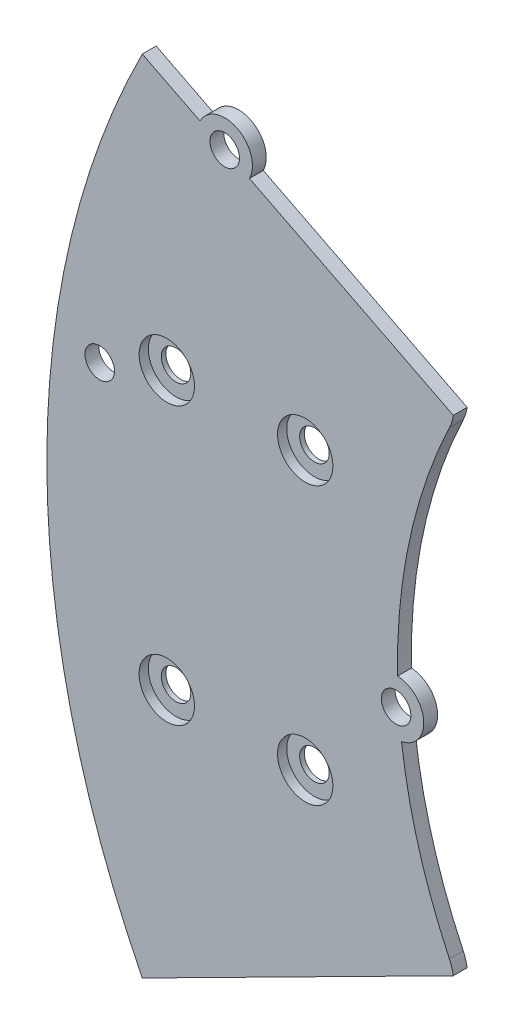
SolidWorks part; units mm, degrees
ref_plane "Front" through (0, 0, 0) normal (0, 0, 1) x (1, 0, 0)
ref_plane "Top" through (0, 0, 0) normal (0, 1, 0) x (1, 0, 0)
ref_plane "Right" through (0, 0, 0) normal (1, 0, 0) x (0, 0, -1)
sketch "Sketch1" plane through (0, 0, 0) normal (0, 0, 1) x (1, 0, 0)
  line L6 (32.7705, 29) -> (-0.1384, 48)
  line L7 (32.7705, -29) -> (-0.1384, -48)
  circle A0 centre (0, 15) radius 1.6
  circle A1 centre (15, 15) radius 1.6
  circle A2 centre (15, -15) radius 1.6
  circle A3 centre (0, -15) radius 1.6
  arc A4 (-0.1384, 48) -> (-0.1384, -48) centre (83, 0) ccw
  arc A5 (32.7705, 29) -> (32.7705, -29) centre (83, 0) ccw
extrude "Boss-Extrude1" add sketch "Sketch1" along normal blind 1.5
fillet "Fillet1" radius 5 4 edges at (32.7705, 29, 0.75) (-0.1384, 48, 0.75) (32.7705, -29, 0.75) (-0.1384, -48, 0.75)
sketch "Sketch2" plane through (0, 0, 1.5) normal (0, 0, 1) x (1, 0, 0)
  line L0 (83, 0) -> (-2.6502, 43.3594)
  line L1 (83, 0) -> (-2.6502, -43.3594)
  line L2 (-2.6502, -43.3594) -> (-16.4497, -74.0903)
  line L3 (-16.4497, -74.0903) -> (122.6028, -61.5432)
  line L4 (122.6028, -61.5432) -> (145.6273, 17.8784)
  line L5 (145.6273, 17.8784) -> (87.9367, 66.5144)
  line L6 (87.9367, 66.5144) -> (-7.0071, 61.211)
  line L7 (-7.0071, 61.211) -> (-2.6502, 43.3594)
extrude "Cut-Extrude1" cut sketch "Sketch2" against normal blind 1.5
sketch "Sketch3" plane through (0, 0, 1.5) normal (0, 0, 1) x (1, 0, 0)
  line L0 (-2.6502, 43.3594) -> (6.2792, 38.839)
  line L1 (-2.6502, 43.3594) -> (31.0524, 26.2979) construction
  line L2 (6.2792, 38.839) -> (-7.2706, 12.0733)
  line L3 (-7.2706, 12.0733) -> (24.8482, -4.1864)
  circle A0 centre (6.2792, 38.839) radius 1.6
  circle A1 centre (-7.2706, 12.0733) radius 1.6
  circle A2 centre (24.8482, -4.1864) radius 1.6
extrude "Cut-Extrude2" cut sketch "Sketch3" against normal blind 1.5
sketch "Sketch4" plane through (0, 0, 1.5) normal (0, 0, 1) x (1, 0, 0)
  circle A0 centre (6.2792, 38.839) radius 1.6
  circle A1 centre (6.2792, 38.839) radius 3
  circle A2 centre (24.8482, -4.1864) radius 1.6
  circle A3 centre (24.8482, -4.1864) radius 3
extrude "Boss-Extrude2" add sketch "Sketch4" against normal up to surface (1.5 mm away) up to face at (-5.6706, 12.0733, 0)
sketch "Sketch5" plane through (0, 0, 1.5) normal (0, 0, 1) x (1, 0, 0)
  circle A0 centre (0, 15) radius 3
  circle A1 centre (15, 15) radius 3
  circle A2 centre (15, -15) radius 3
  circle A3 centre (0, -15) radius 3
extrude "Cut-Extrude3" cut sketch "Sketch5" against normal blind 1
